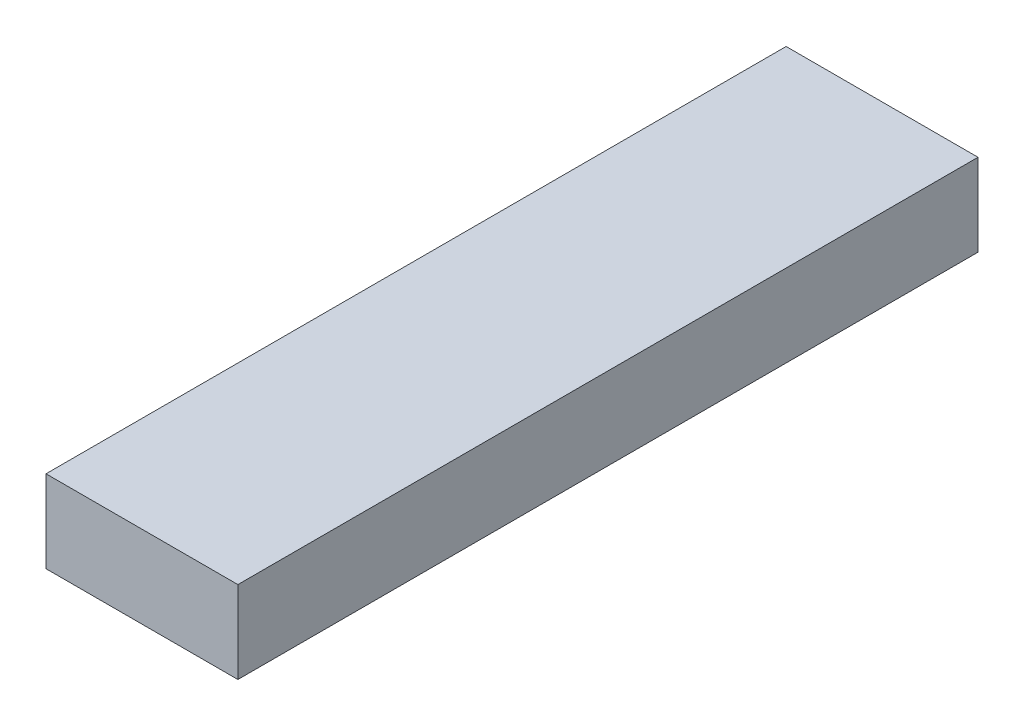
SolidWorks part; units mm, degrees
material "Balsa"
ref_plane "Front Plane" through (0, 0, 0) normal (0, 0, 1) x (1, 0, 0)
ref_plane "Top Plane" through (0, 0, 0) normal (0, 1, 0) x (1, 0, 0)
ref_plane "Right Plane" through (0, 0, 0) normal (1, 0, 0) x (0, 0, -1)
sketch "Sketch2" plane through (0, 0, 0) normal (0, 1, 0) x (1, 0, 0)
  line L1 (0, 0) -> (88.9, 0)
  line L2 (0, 0) -> (0, 342.9)
  line L3 (0, 342.9) -> (88.9, 342.9)
  line L4 (88.9, 0) -> (88.9, 342.9)
extrude "Boss-Extrude3" add sketch "Sketch2" along normal blind 38.1
